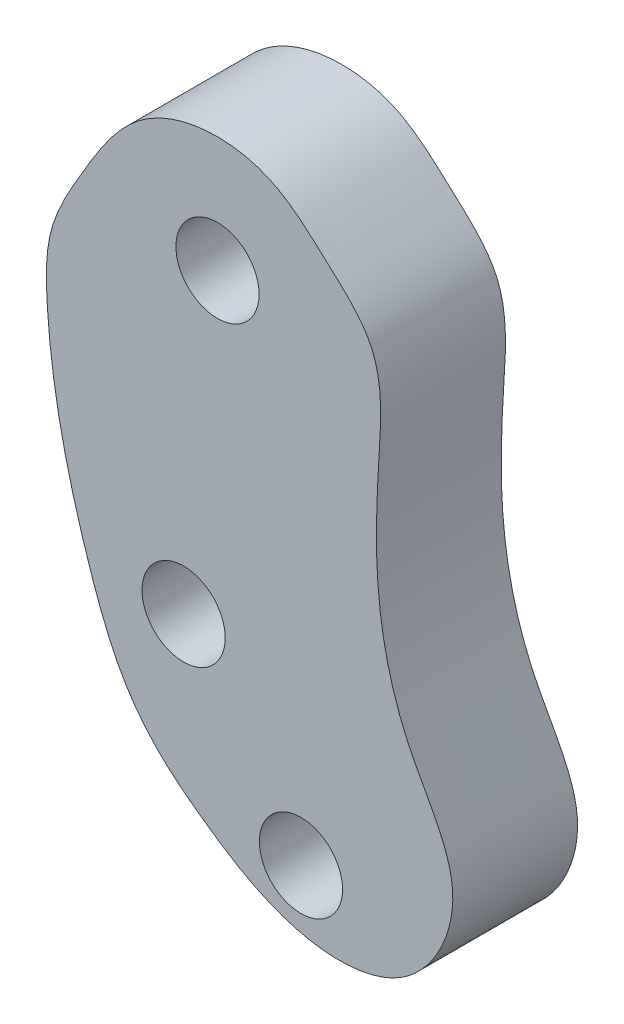
SolidWorks part; units mm, degrees
ref_plane "Спереди" through (0, 0, 0) normal (0, 0, 1) x (1, 0, 0)
ref_plane "Сверху" through (0, 0, 0) normal (0, 1, 0) x (1, 0, 0)
ref_plane "Справа" through (0, 0, 0) normal (1, 0, 0) x (0, 0, -1)
other "Configuration Table"
sketch "Sketch1" plane through (0, 0, 0) normal (0, 0, 1) x (1, 0, 0)
  circle A0 centre (-10.5938, 31.8638) radius 1
  circle A1 centre (-8.5872, 20.4791) radius 1
  circle A2 centre (-11.4086, 24.3035) radius 1
  spline S0 degree 3 poles (-13.7826, 32.3865) (-12.9403, 33.7945) (-11.3667, 34.7308) (-9.4508, 34.7412) (-8.0127, 33.3834) (-6.5657, 32.1077) (-6.7328, 29.7293) (-6.8561, 27.1076) (-6.2226, 24.2635) (-4.4146, 21.8576) (-5.7849, 19.0557) (-8.6714, 18.7909) (-10.5623, 19.9425) (-11.9646, 21.0354) (-12.9779, 22.25) (-13.7013, 24.1421) (-14.3895, 26.5454) (-14.704, 28.7161) (-14.7359, 30.7557) (-13.7826, 32.3865) (-12.9403, 33.7945) (-11.3667, 34.7308) knots -0.137032 -0.100916 -0.054541 0 0.016845 0.079936 0.121675 0.162279 0.214973 0.284203 0.360988 0.426471 0.491284 0.546187 0.620381 0.650125 0.677948 0.736183 0.798042 0.862968 0.899084 0.945459 1 1.016845 1.079936 1.121675 only from (-12.4811, 34.0371) to (-12.4811, 34.0371)
  point P3 (-5.5146, 27.0112)
  point P12 (-10.6376, 31.4582)
  point P14 (-12.4819, 16.085)
  point P16 (-9.2454, 20.0295)
  point P18 (-13.4925, 18.3228)
  point P20 (-9.6426, 15.0503)
  point P22 (0, 0)
  point P23 (-4.2767, 19.3575)
  point P24 (0, 0)
  point P25 (-4.9504, 18.2506)
  point P26 (0, 0)
  point P28 (0, 0)
  point P30 (0, 0)
  point P31 (-10.3163, 14.7616)
  point P32 (0, 0)
  point P33 (-14.5272, 18.2747)
  point P34 (-6.4904, 16.0609)
  point P35 (-9.2576, 15.7481)
  point P36 (-4.9986, 17.7934)
  point P37 (-6.7792, 17.2159)
  point P38 (-9.3538, 16.8069)
  point P39 (-12.3135, 17.3844)
  point P40 (-13.8053, 18.7559)
  point P41 (-15.0325, 20.7531)
  point P42 (-4.8043, 22.2078)
  point P43 (-5.6499, 27.6539)
  point P44 (-5.1764, 24.6771)
  point P46 (-6.2926, 29.7172)
  point P48 (-6.6986, 31.4582)
  point P50 (-7.984, 33.3705)
  point P52 (-9.337, 34.3853)
  point P54 (0, 0)
  point P56 (-5.9882, 29.379)
  point P58 (-5.2102, 24.1873)
  point P59 (-12.4811, 34.0371)
  point P60 (-4.9396, 21.7343)
  point P61 (-14.2857, 33.3357)
  point P62 (-5.9544, 18.487)
  point P63 (0, 0)
  point P64 (-13.2947, 19.5356)
  point P65 (-14.2756, 21.8696)
  point P66 (-14.7492, 24.1873)
  point P67 (-13.7344, 21.9711)
  point P68 (-14.8507, 24.7786)
  point P69 (-15.3242, 26.267)
  point P70 (-14.3094, 25.1845)
  point P71 (-15.4257, 28.2966)
  point P72 (-14.8507, 26.8082)
  point P73 (-15.9669, 30.0217)
  point P74 (-13.7006, 19.4003)
  point P75 (-15.764, 28.5333)
  point P76 (-15.5948, 32.1189)
  point P77 (0, 0)
  point P78 (0, 0)
  point P79 (-12.8334, 34.0818)
  point P80 (-12.1852, 17.3591)
  point P81 (-10.8925, 19.0856)
  point P82 (-12.0687, 20.7214)
  point P83 (-12.6771, 21.9517)
  point P84 (-13.6505, 24.1013)
  point P85 (-14.3241, 26.5157)
  point P86 (-15.1287, 28.6231)
  point P87 (-15.3203, 30.1367)
  point P88 (-14.6881, 29.1213)
  point P89 (-14.803, 30.6731)
  point P90 (-14.3624, 32.2633)
  point P91 (-14.5025, 31.113)
  point P92 (-13.2465, 33.4091)
  point P93 (-14.6202, 30.5831)
  point P94 (-13.8352, 32.2905)
  point P95 (0, 0)
  point P96 (0, 0)
  point P97 (-8.3146, 18.7491)
  point P98 (-11.0246, 20.3201)
  point P99 (-11.956, 21.0851)
  point P100 (-6.121, 19.3887)
  point P101 (-8.3146, 19.0184)
  point P102 (-5.9511, 24.1873)
  point P103 (-6.7327, 27.1989)
  point P104 (-6.7065, 30.0041)
  point P105 (-6.9028, 32.1303)
  point P106 (-11.4086, 24.3035)
  dimension "D1" = 2
  dimension "D2" = 7.604
  dimension "D3" = 11.5602
  dimension "D4" = 4.7525
extrude "Boss-Extrude1" add sketch "Sketch1" along normal blind 3
ref_plane "Plane1" through (0, 0, 3) normal (0, 0, 1) x (1, 0, 0)
equation "\"R small\"= 2"
equation "\"R big\"= 4"
equation "\"width\"= 0.6"
equation "\"border width\"= 1"
equation "\"thickness\"= 3"
equation "\"D1@Boss-Extrude1\"=\"thickness\""
equation "\"D1@Sketch2\"=\"R small\""
equation "\"D1@Sketch1\"=\"R small\""
